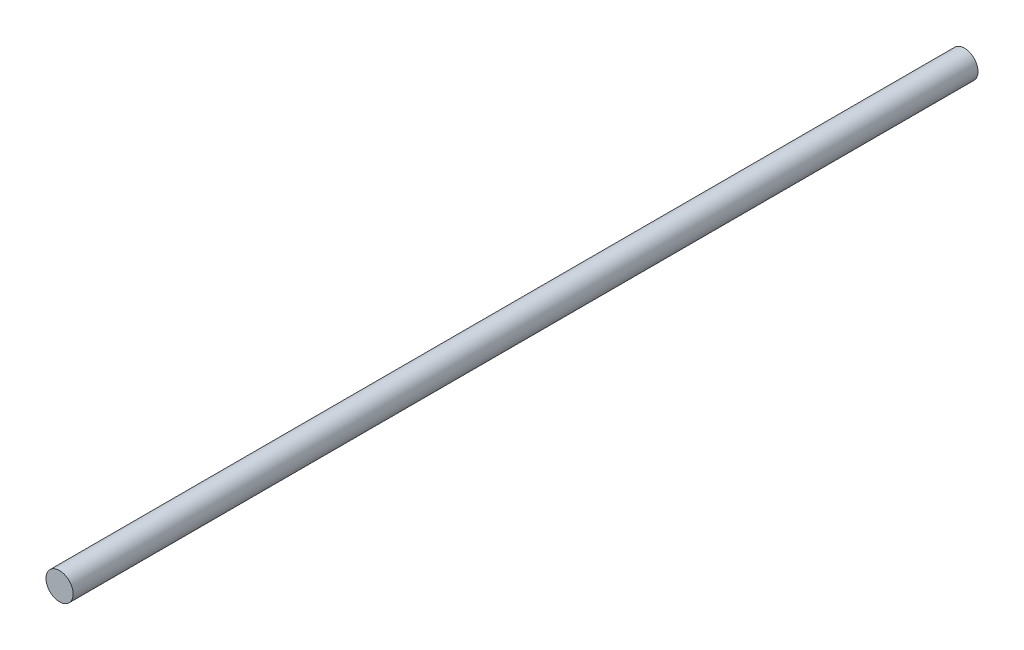
SolidWorks part; units mm, degrees
ref_plane "Front Plane" through (0, 0, 0) normal (0, 0, 1) x (1, 0, 0)
ref_plane "Top Plane" through (0, 0, 0) normal (0, 1, 0) x (1, 0, 0)
ref_plane "Right Plane" through (0, 0, 0) normal (1, 0, 0) x (0, 0, -1)
sketch "Sketch1" plane through (0, 0, 0) normal (0, 0, 1) x (1, 0, 0)
  circle A0 centre (0, 0) radius 1.5
extrude "Boss-Extrude1" add sketch "Sketch1" along normal blind 100
